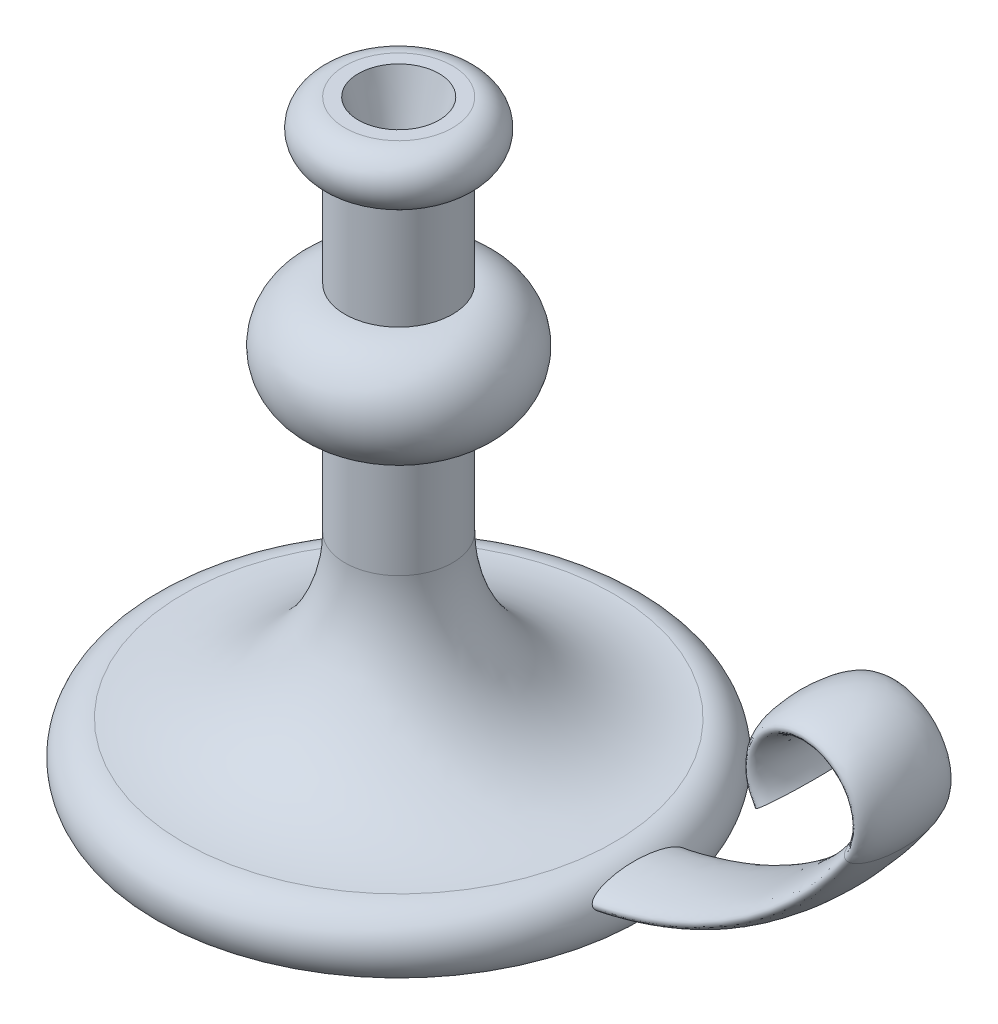
SolidWorks part; units mm, degrees
ref_plane "Front Plane" through (0, 0, 0) normal (0, 0, 1) x (1, 0, 0)
ref_plane "Top Plane" through (0, 0, 0) normal (0, 1, 0) x (1, 0, 0)
ref_plane "Right Plane" through (0, 0, 0) normal (1, 0, 0) x (0, 0, -1)
sketch "Sketch1" plane through (0, 0, 0) normal (0, 0, 1) x (1, 0, 0)
  line L0 (0, 0) -> (0, 220)
  line L1 (0, 220) -> (20, 220)
  line L2 (0, 0) -> (90, 0)
  line L3 (20, 200) -> (20, 160)
  line L4 (20, 120) -> (20, 80)
  arc A0 (20, 220) -> (20, 200) centre (20, 210) cw
  arc A1 (20, 160) -> (20, 120) centre (20, 140) cw
  arc A2 (20, 80) -> (80, 20) centre (80, 80) ccw
  arc A3 (80, 20) -> (90, 0) centre (80, 7.5) cw
  dimension "D4" = 10
  dimension "D5" = 20
  dimension "D6" = 40
  dimension "D7" = 60
  dimension "D8" = 12.5
  dimension "D1" = 220
  dimension "D2" = 20
  dimension "D3" = 90
  dimension "D9" = 80
revolve "Revolve1" add sketch "Sketch1" angle 360 about L0
sketch "Sketch2" plane through (0, 0, 0) normal (0, 0, 1) x (1, 0, 0)
  line L0 (0, 10) -> (60, 10)
  line L1 (0, 227.4356) -> (0, 175.1288) construction
  line L2 (0, 164) -> (0, 92) construction
  arc A0 (60, 10) -> (183.5921, 75) centre (60, 160) ccw
  arc A1 (183.5921, 75) -> (150.6342, 75) centre (167.1131, 86.3333) ccw
  point P10 (183.5921, 247.1188)
  point P11 (0, 64.5194)
  dimension "D2" = 65
  dimension "D3" = 20
  dimension "D4" = 150
  dimension "D1" = 60
  dimension "D5" = 10
sketch "Sketch3" plane through (0, 0, 0) normal (1, 0, 0) x (0, 0, -1)
  ellipse E0 centre (0, 10) end of major axis (-17.5, 10) minor radius 5
  point P1 (0, 0)
  dimension "D1" = 35
  dimension "D2" = 10
sweep "Sweep1" add profiles "Sketch3" path "Sketch2"
sketch "Sketch4" plane through (0, 220, 0) normal (0, 1, 0) x (1, 0, 0)
  circle A0 centre (0, 0) radius 15
  dimension "D1" = 30
extrude "Cut-Extrude1" cut sketch "Sketch4" against normal blind 25 draft 15
